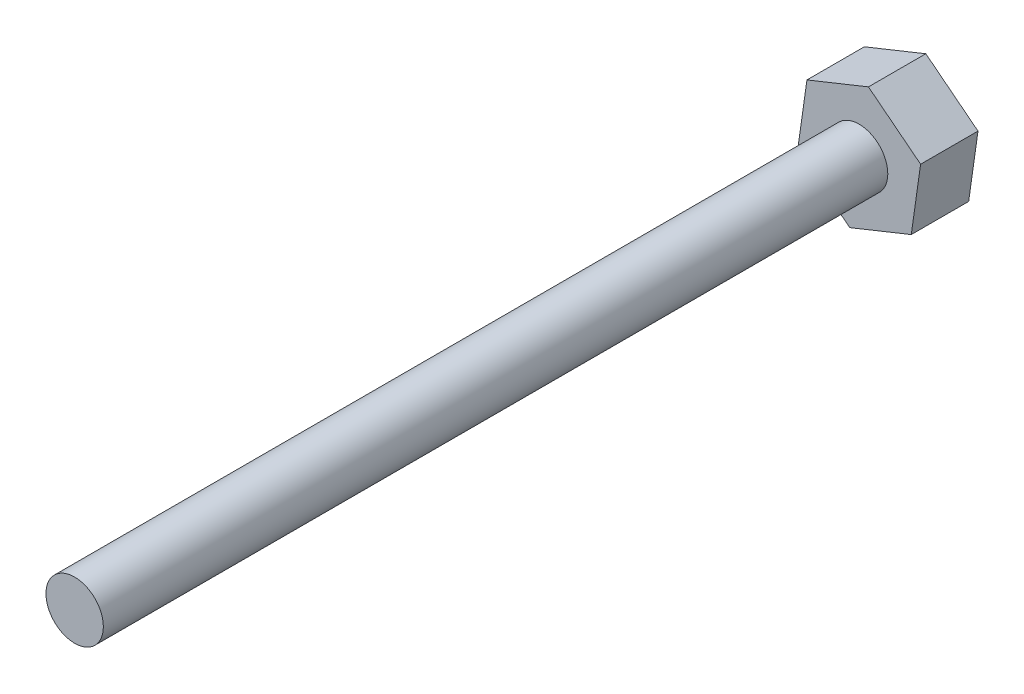
SolidWorks part; units mm, degrees
ref_plane "Front Plane" through (0, 0, 0) normal (0, 0, 1) x (1, 0, 0)
ref_plane "Top Plane" through (0, 0, 0) normal (0, 1, 0) x (1, 0, 0)
ref_plane "Right Plane" through (0, 0, 0) normal (1, 0, 0) x (0, 0, -1)
sketch "Sketch1" plane through (0, 0, 0) normal (0, 0, 1) x (1, 0, 0)
  line L1 (-2.726, 2.1375) -> (-3.2141, -1.2921)
  line L2 (-3.2141, -1.2921) -> (-0.4881, -3.4295)
  line L3 (-0.4881, -3.4295) -> (2.726, -2.1375)
  line L4 (2.726, -2.1375) -> (3.2141, 1.2921)
  line L5 (3.2141, 1.2921) -> (0.4881, 3.4295)
  line L6 (0.4881, 3.4295) -> (-2.726, 2.1375)
  circle A0 centre (0, 0) radius 3 construction
  dimension "D1" = 6
extrude "Boss-Extrude1" add sketch "Sketch1" along normal blind 3
sketch "Sketch2" plane through (0, 0, 0) normal (0, 0, 1) x (1, 0, 0)
  circle A0 centre (0, 0) radius 1.5
  dimension "D1" = 3
sketch "Sketch3" plane through (0, 0, 3) normal (0, 0, 1) x (1, 0, 0)
  circle A0 centre (0, 0) radius 1.5
  dimension "D1" = 3
extrude "Boss-Extrude2" add sketch "Sketch3" along normal blind 41
